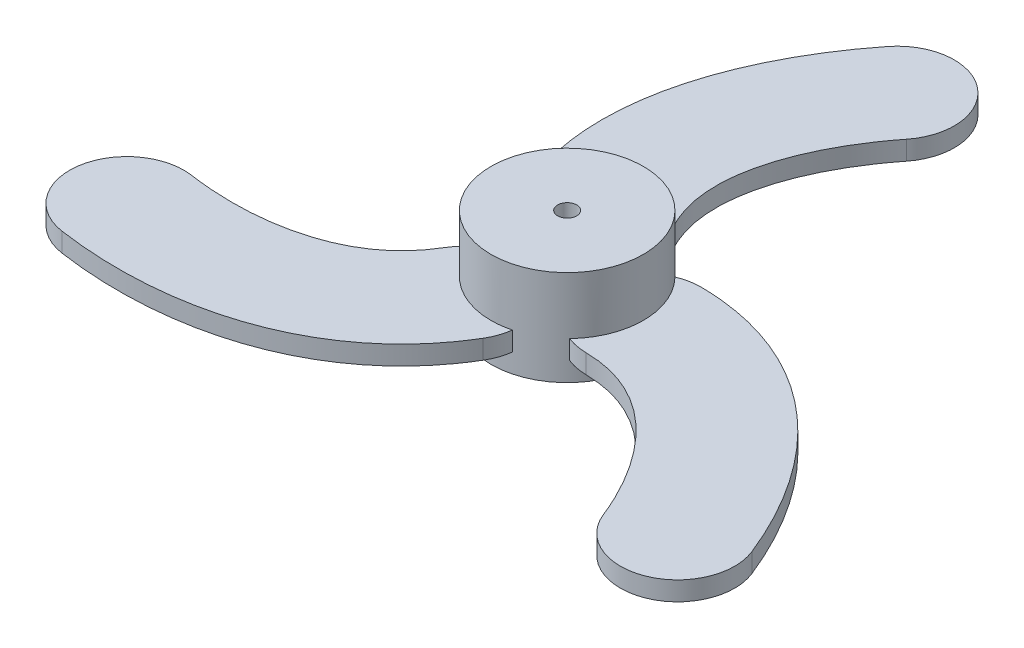
SolidWorks part; units mm, degrees
ref_plane "Front Plane" through (0, 0, 0) normal (0, 0, 1) x (1, 0, 0)
ref_plane "Top Plane" through (0, 0, 0) normal (0, 1, 0) x (1, 0, 0)
ref_plane "Right Plane" through (0, 0, 0) normal (1, 0, 0) x (0, 0, -1)
sketch "Sketch1" plane through (0, 0, 0) normal (0, 1, 0) x (1, 0, 0)
  circle A0 centre (0, 0) radius 4
  dimension "D1" = 8
extrude "Boss-Extrude1" add sketch "Sketch1" along normal blind 5
sketch "Sketch2" plane through (0, 0, 0) normal (0, 1, 0) x (1, 0, 0)
  circle A0 centre (0, 0) radius 20 construction
  arc A2 (3.9629, -2.9709) -> (2.895, -2.7603) centre (3.9999, 0.0288) cw
  arc A3 (11.7746, -9.8785) -> (17.3507, -7.6634) centre (14.5626, -8.771) ccw
  arc A4 (2.8549, 2.8017) -> (4.0369, 3.0286) centre (3.9999, 0.0288) cw
  circle A5 centre (0, 0) radius 4
  arc A6 (2.895, -2.7603) -> (2.8549, 2.8017) centre (0, 0) ccw
  arc A7 (2.895, -2.7603) -> (2.8549, 2.8017) centre (3.9999, 0.0288) cw construction
  arc A8 (2.8549, 2.8017) -> (2.895, -2.7603) centre (0, 0) ccw construction
  arc A9 (-3.838, -1.127) -> (0.9989, -3.8733) centre (0, 0) ccw
  arc A10 (0.9989, -3.8733) -> (0.6044, -5.0103) centre (-1.975, -3.4784) cw
  arc A11 (-14.4424, -5.2578) -> (-15.312, -11.1944) centre (-14.8772, -8.2261) ccw
  arc A12 (-4.5544, -1.9465) -> (-3.838, -1.127) centre (-1.975, -3.4784) cw
  arc A13 (0.943, 3.8873) -> (-3.8538, 1.0715) centre (0, 0) ccw
  arc A14 (-3.8538, 1.0715) -> (-4.6413, 1.9817) centre (-2.0249, 3.4496) cw
  arc A15 (2.6678, 15.1364) -> (-2.0387, 18.8578) centre (0.3146, 16.9971) ccw
  arc A16 (0.5914, 4.9175) -> (0.943, 3.8873) centre (-2.0249, 3.4496) cw
  spline S0 degree 3 poles (3.9999, 0.0288) (9.2482, -0.0358) (12.8166, -4.3758) (14.5626, -8.771) knots 0 0 0 0 1 1 1 1 construction
  spline S1 degree 1 poles (3.9629, -2.9709) (11.7746, -9.8785) knots 0 0 1 1 construction
  spline S2 degree 3 poles (3.9629, -2.9709) (4.1822, -2.9736) (4.6284, -3.0021) (5.4504, -3.142) (6.4199, -3.4628) (7.5191, -4.0747) (8.912, -5.1875) (10.4732, -7.1007) (11.4012, -8.9387) (11.7746, -9.8785) knots 0 0 0 0 0.0625 0.125 0.25 0.375 0.5 0.75 1 1 1 1
  spline S3 degree 1 poles (4.0369, 3.0286) (17.3507, -7.6634) knots 0 0 1 1 construction
  spline S4 degree 3 poles (4.0369, 3.0286) (4.4617, 3.0234) (5.3187, 2.9687) (6.9542, 2.692) (9.6408, 1.7965) (12.8101, -0.4194) (15.1163, -3.2891) (16.5316, -5.7683) (17.0952, -7.0202) (17.3507, -7.6634) knots 0 0 0 0 0.0625 0.125 0.25 0.5 0.75 0.875 1 1 1 1
  spline S5 degree 3 poles (0.6044, -5.0103) (0.3875, -5.3756) (-0.0884, -6.0905) (-1.1457, -7.3685) (-3.2646, -9.2474) (-6.7682, -10.8842) (-10.4066, -11.4465) (-13.2613, -11.4327) (-14.6272, -11.2948) (-15.312, -11.1944) knots 0 0 0 0 0.0625 0.125 0.25 0.5 0.75 0.875 1 1 1 1
  spline S6 degree 3 poles (-4.5544, -1.9465) (-4.6664, -2.1351) (-4.9141, -2.5072) (-5.4463, -3.1492) (-6.2089, -3.8284) (-7.2883, -4.4743) (-8.9485, -5.1243) (-11.386, -5.5197) (-13.4418, -5.4044) (-14.4424, -5.2578) knots 0 0 0 0 0.0625 0.125 0.25 0.375 0.5 0.75 1 1 1 1
  spline S7 degree 3 poles (-4.6413, 1.9817) (-4.8492, 2.3523) (-5.2303, 3.1218) (-5.8085, 4.6765) (-6.3762, 7.4509) (-6.0419, 11.3035) (-4.7097, 14.7357) (-3.2704, 17.2009) (-2.4679, 18.3149) (-2.0387, 18.8578) knots 0 0 0 0 0.0625 0.125 0.25 0.5 0.75 0.875 1 1 1 1
  spline S8 degree 3 poles (0.5914, 4.9175) (0.4841, 5.1087) (0.2858, 5.5093) (-0.0042, 6.2912) (-0.2111, 7.2913) (-0.2307, 8.5491) (0.0365, 10.3118) (0.9128, 12.6204) (2.0405, 14.3431) (2.6678, 15.1364) knots 0 0 0 0 0.0625 0.125 0.25 0.375 0.5 0.75 1 1 1 1
  point P33 (0, 0)
  dimension "D1" = 40
  dimension "D2" = 3
  dimension "D3" = 3
  dimension "D4" = 0
  dimension "D5" = 3
extrude "Boss-Extrude2" add sketch "Sketch2" along normal blind 1 from offset 1
sketch "Sketch3" plane through (0, 5, 0) normal (0, 1, 0) x (1, 0, 0)
  circle A0 centre (0, 0) radius 0.5
  dimension "D1" = 1
extrude "Cut-Extrude1" cut sketch "Sketch3" against normal through all both and the other way through all
